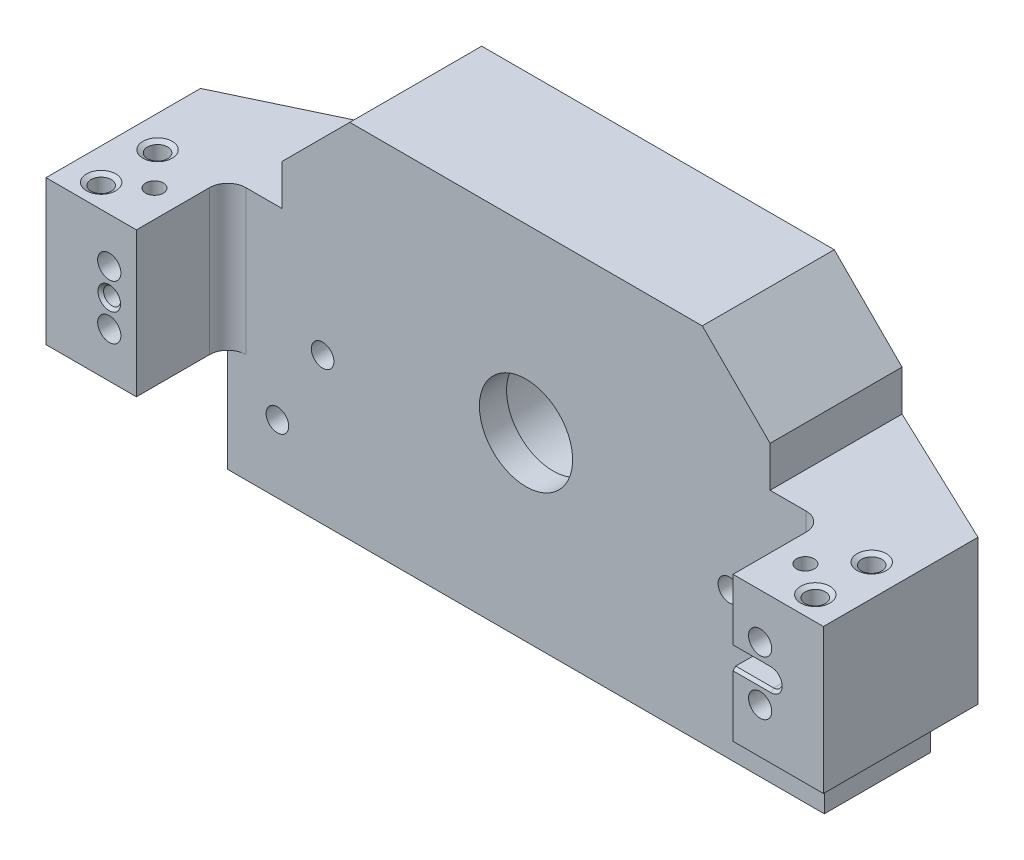
SolidWorks part; units mm, degrees
material "6061-T6 Al"
ref_plane "Front" through (0, 0, 0) normal (0, 0, 1) x (1, 0, 0)
ref_plane "Top" through (0, 0, 0) normal (0, 1, 0) x (1, 0, 0)
ref_plane "Right" through (0, 0, 0) normal (1, 0, 0) x (0, 0, -1)
sketch "Sketch2" plane through (0, 0, 0) normal (0, 1, 0) x (1, 0, 0)
  line L0 (-54.61, -12.7) -> (-54.61, 9.017)
  line L1 (-54.61, 9.017) -> (-34.29, 9.017)
  line L2 (34.29, 18.669) -> (-34.29, 18.669)
  line L3 (-34.29, 9.017) -> (-34.29, 18.669)
  line L4 (34.29, 18.669) -> (34.29, 9.017)
  line L5 (34.29, 9.017) -> (54.61, 9.017)
  line L6 (54.61, 9.017) -> (54.61, -12.7)
  line L7 (-54.61, -12.7) -> (-41.91, -12.7)
  line L8 (-41.91, -12.7) -> (-41.91, 0.127)
  line L9 (-41.91, 0.127) -> (41.91, 0.127)
  line L10 (41.91, 0.127) -> (41.91, -12.7)
  line L11 (41.91, -12.7) -> (54.61, -12.7)
  dimension "D1" = 83.82
  dimension "D2" = 109.22
  dimension "D3" = 31.369
  dimension "D4" = 18.542
  dimension "D5" = 41.91
  dimension "D6" = 18.669
  dimension "D7" = 34.29
  dimension "D8" = 9.652
extrude "Extrude1" add sketch "Sketch2" along normal blind 20.32
sketch "Sketch19" plane through (0, 20.32, 0) normal (0, 1, 0) x (1, 0, 0)
  line L0 (54.61, 9.017) -> (34.29, 9.017) construction
  line L1 (34.29, 9.017) -> (34.29, 18.669) construction
  line L2 (-34.29, 18.669) -> (-34.29, 9.017) construction
  line L3 (-34.29, 9.017) -> (-54.61, 9.017) construction
  line L4 (54.61, 9.017) -> (34.29, 9.017)
  line L5 (34.29, 9.017) -> (34.29, 18.669)
  line L6 (-34.29, 18.669) -> (-34.29, 9.017)
  line L7 (-34.29, 9.017) -> (-54.61, 9.017)
  line L8 (-34.29, 18.669) -> (-54.61, 9.017)
  line L9 (34.29, 18.669) -> (54.61, 9.017)
extrude "Extrude2" add sketch "Sketch19" against normal up to surface (20.32 mm away) up to face at (0, 0, -1.905)
sketch "Sketch24" plane through (0, 20.32, 0) normal (0, 1, 0) x (1, 0, 0)
  line L0 (-41.91, 0.127) -> (41.91, 0.127) construction
  line L1 (34.29, 18.669) -> (-34.29, 18.669)
  line L2 (34.29, 18.669) -> (34.29, 0.127)
  line L3 (34.29, 0.127) -> (-34.29, 0.127)
  line L4 (-34.29, 18.669) -> (-34.29, 0.127)
extrude "Extrude3" add sketch "Sketch24" along normal blind 15.24
sketch "Sketch25" plane through (0, 0, 0) normal (0, -1, 0) x (1, 0, 0)
  line L0 (-41.91, -0.127) -> (41.91, -0.127) construction
  line L1 (-34.29, -18.669) -> (34.29, -18.669)
  line L2 (-41.91, -0.127) -> (-41.91, -15.0495)
  line L3 (-41.91, -0.127) -> (41.91, -0.127)
  line L4 (-41.91, 12.7) -> (-41.91, -0.127) construction
  line L5 (-41.91, -15.0495) -> (-34.29, -18.669)
  line L6 (41.91, -0.127) -> (41.91, -15.0495)
  line L7 (41.91, -0.127) -> (41.91, 12.7) construction
  line L8 (54.61, -9.017) -> (34.29, -18.669) construction
  line L9 (41.91, -15.0495) -> (34.29, -18.669)
  line L10 (-34.29, -18.669) -> (-54.61, -9.017) construction
extrude "Extrude4" add sketch "Sketch25" along normal blind 15.24
sketch "Sketch38" plane through (0, 0, -18.669) normal (0, 0, -1) x (-1, 0, 0)
  circle A0 centre (0, 10.16) radius 17.78
  circle A1 centre (0, 10.16) radius 25.4 construction
  dimension "D1" = 35.56
  dimension "D2" = 50.8
  dimension "D3" = 10.16
extrude "Spherical washer Center Relief" cut sketch "Sketch38" against normal blind 0.762
hole_wizard "Tapped Hole For 1/4-20 Helicoil" positions "Sketch27" profile "Sketch26" tap size "1/4-20" standard "Helicoil® Inch"
sketch "Sketch27" plane through (0, -15.24, 0) normal (0, -1, 0) x (1, 0, 0)
  point P0 (28.575, -6.35)
  point P3 (-28.575, -6.35)
  dimension "D1" = 57.15
  dimension "D2" = 28.575
  dimension "D3" = 6.35
sketch "Sketch26" plane through (28.575, -15.24, -6.35) normal (1, 0, 0) x (0, 0, -1)
  line L0 (0, 0) -> (0, 22.6038)
  line L1 (0, 22.6038) -> (3.3782, 20.574)
  line L2 (3.3782, 20.574) -> (3.3782, 11.684)
  line L3 (3.3782, 11.684) -> (4.0475, 11.684)
  line L5 (4.0475, 11.684) -> (4.0475, 0.0165)
  line L6 (4.0475, 0.0165) -> (4.064, 0)
  line L7 (4.064, 0) -> (0, 0)
  line L8 (-4.0475, 0.0165) -> (-4.064, 0) construction
  line L10 (0, 22.6038) -> (-3.3782, 20.574) construction
  line L11 (0, -6.35) -> (0, 107.95) construction
  dimension "Tap Drill Dia." = 6.7564
  dimension "Tap Drill Depth" = 20.574
  dimension "Thread Major Dia." = 8.095
  dimension "Thread Depth" = 11.684
  dimension "Near C'Sink Dia." = 8.128
  dimension "Near C'Sink Angle" = 90
  dimension "Drill Angle" = 118
sketch "Sketch30" plane through (0, -15.24, 0) normal (0, -1, 0) x (1, 0, 0)
  line L0 (-33.3375, -13.97) -> (-36.5125, -13.97) construction
  line L1 (-33.3375, -15.5651) -> (-36.5125, -15.5651)
  line L2 (-33.3375, -12.3749) -> (-36.5125, -12.3749)
  circle A0 centre (34.925, -13.97) radius 1.5951
  arc A1 (-33.3375, -15.5651) -> (-33.3375, -12.3749) centre (-33.3375, -13.97) ccw
  arc A2 (-36.5125, -12.3749) -> (-36.5125, -15.5651) centre (-36.5125, -13.97) ccw
  circle A3 centre (28.575, -6.35) radius 4.0475 construction
  circle A4 centre (28.575, -6.35) radius 3.3782 construction
  circle A5 centre (-28.575, -6.35) radius 3.3782 construction
  point P4 (-34.925, -13.97)
  dimension "D1" = 6.35
  dimension "D4" = 3.1902
  dimension "D3" = 6.35
  dimension "D2" = 7.62
  dimension "D6" = 3.175
extrude "Pin & Slot Holes" cut sketch "Sketch30" against normal blind 9.525
hole_wizard "#4 Clearance Hole1" positions "Sketch29" profile "Sketch28" hole size "#4" standard "Ansi Inch" end condition through all
sketch "Sketch29" plane through (0, 0, -18.669) normal (0, 0, -1) x (-1, 0, 0)
  line L0 (-31.9532, 5.334) -> (-25.1968, 5.334) construction
  line L1 (25.1968, 5.334) -> (31.9532, 5.334) construction
  point P0 (-28.575, 5.334)
  point P4 (28.575, 5.334)
sketch "Sketch28" plane through (28.575, 5.334, -18.669) normal (1, 0, 0) x (0, 1, 0)
  line L0 (0, 0) -> (0, 31.369)
  line L1 (0, 31.369) -> (1.5875, 31.369)
  line L2 (1.5875, 31.369) -> (1.5875, 0)
  line L5 (1.5875, 0) -> (0, 0)
  line L11 (0, -6.35) -> (0, 107.95) construction
  dimension "Thru Hole Dia." = 3.175
  dimension "Thru Hole Depth" = 31.369
hole_wizard "#4 Clearance Hole2" positions "Sketch33" profile "Sketch32" hole size "#4" standard "Ansi Inch" end condition through all
sketch "Sketch33" plane through (0, 0, -18.669) normal (0, 0, -1) x (-1, 0, 0)
  line L0 (36.5125, -5.715) -> (33.3375, -5.715) construction
  line L1 (-34.925, -5.715) -> (-34.925, -15.24) construction
  line L2 (34.925, -5.715) -> (-34.925, -5.715) construction
  point P0 (-34.925, -5.715)
  point P1 (34.925, -5.715)
sketch "Sketch32" plane through (34.925, -5.715, -18.669) normal (1, 0, 0) x (0, 1, 0)
  line L0 (0, 0) -> (0, 31.369)
  line L1 (0, 31.369) -> (1.5875, 31.369)
  line L2 (1.5875, 31.369) -> (1.5875, 0)
  line L5 (1.5875, 0) -> (0, 0)
  line L11 (0, -6.35) -> (0, 107.95) construction
  dimension "Thru Hole Dia." = 3.175
  dimension "Thru Hole Depth" = 31.369
hole_wizard "CBORE for #4 Socket Head Cap Screw1" positions "Sketch16" profile "Sketch15" counterbore size "#4" standard "Ansi Inch" end condition through all
sketch "Sketch16" plane through (-10.4024, -1.8195, -18.669) normal (0, 0, -1) x (-1, 0, 0)
  line L0 (44.2076, 11.9795) -> (-65.0124, 11.9795) construction
  line L4 (35.3176, 8.1695) -> (35.3176, 11.9795) construction
  line L5 (35.3176, 11.9795) -> (35.3176, 15.7895) construction
  line L7 (-56.1224, 8.1695) -> (-56.1224, 11.9795) construction
  line L8 (-56.1224, 11.9795) -> (-56.1224, 15.7895) construction
  line L9 (44.2076, 22.1395) -> (44.2076, 1.8195) construction
  line L10 (-65.0124, 22.1395) -> (-65.0124, 1.8195) construction
  point P1 (35.3176, 8.1695)
  point P3 (35.3176, 15.7895)
  point P5 (-56.1224, 8.1695)
  point P7 (-56.1224, 15.7895)
  dimension "D1" = 7.62
  dimension "D2" = 7.62
  dimension "D3" = 91.44
  dimension "D4" = 45.72
sketch "Sketch15" plane through (-45.72, 6.35, -18.669) normal (1, 0, 0) x (0, 1, 0)
  line L0 (0, 0) -> (0, 31.369)
  line L1 (0, 31.369) -> (1.6319, 31.369)
  line L3 (1.6319, 31.369) -> (1.6319, 18.2372)
  line L4 (1.6319, 18.2372) -> (2.9718, 18.2372)
  line L5 (2.9718, 18.2372) -> (2.9718, 0)
  line L7 (2.9718, 0) -> (0, 0)
  line L11 (0, -6.35) -> (0, 107.95) construction
  dimension "Thru Hole Dia." = 3.2639
  dimension "Thru Hole Depth" = 31.369
  dimension "C'Bore Dia." = 5.9436
  dimension "C'Bore Depth" = 18.2372
hole_wizard "Tapped Hole for 1/2-13  Helicoil1" positions "Sketch23" profile "Sketch22" tap size "1/2-13" standard "Helicoil® Inch" end condition through all
sketch "Sketch23" plane through (0, 0, -18.669) normal (0, 0, -1) x (-1, 0, 0)
  point P0 (0, 10.16)
  dimension "D1" = 10.16
sketch "Sketch22" plane through (0, 10.16, -18.669) normal (1, 0, 0) x (0, 1, 0)
  line L0 (0, 0) -> (0, 31.369)
  line L1 (6.5481, 30.3527) -> (8.3083, 31.369)
  line L2 (7.6733, 14.732) -> (6.5481, 14.732)
  line L3 (6.5481, 14.732) -> (6.5481, 30.3527)
  line L5 (7.6733, 14.732) -> (7.6733, 0.3666)
  line L6 (7.6733, 0.3666) -> (8.3083, 0)
  line L7 (8.3083, 0) -> (0, 0)
  line L8 (-7.6733, 0.3666) -> (-8.3083, 0) construction
  line L11 (0, -6.35) -> (0, 107.95) construction
  line L12 (8.3083, 31.369) -> (0, 31.369)
  line L13 (-6.5481, 30.3527) -> (-8.3083, 31.369) construction
  dimension "Thru Tap Drill Dia." = 13.0962
  dimension "Thru Tap Drill Depth" = 31.369
  dimension "Thread Major Dia." = 15.3467
  dimension "Thread Depth" = 14.732
  dimension "Near C'Sink Dia." = 16.6167
  dimension "Near C'Sink Angle" = 120
  dimension "Far C'Sink Dia." = 16.6167
  dimension "Far C'Sink Angle" = 120
hole_wizard "#40 (0.098) Diameter Hole0" positions "Sketch37" profile "Sketch36" hole size "#40" standard "Ansi Inch" end condition through all
sketch "Sketch37" plane through (0, 20.32, 0) normal (0, 1, 0) x (-1, 0, 0)
  line L0 (45.72, 12.7) -> (45.72, -0.4318) construction
  line L1 (54.61, 12.7) -> (41.91, 12.7) construction
  line L2 (-45.72, 12.7) -> (-45.72, -0.4318) construction
  point P0 (45.72, 6.35)
  point P6 (-45.72, 6.35)
  dimension "D1" = 6.35
sketch "Sketch36" plane through (-45.72, 20.32, 6.35) normal (1, 0, 0) x (0, 0, 1)
  line L0 (0, 0) -> (0, 35.56)
  line L1 (0, 35.56) -> (1.2446, 35.56)
  line L2 (1.2446, 35.56) -> (1.2446, 0)
  line L5 (1.2446, 0) -> (0, 0)
  line L11 (0, -6.35) -> (0, 107.95) construction
  dimension "Thru Hole Dia." = 2.4892
  dimension "Thru Hole Depth" = 35.56
hole_wizard "#4-40 Tapped Hole1" positions "Sketch21" profile "Sketch20" tap size "#4-40" standard "Ansi Inch" end condition up to next
sketch "Sketch21" plane through (0, 20.32, 0) normal (0, 1, 0) x (-1, 0, 0)
  point P0 (50.165, 9.398)
  point P2 (50.165, 1.4732)
  point P4 (-50.165, 1.4732)
  point P6 (-50.165, 9.398)
  dimension "D1" = 100.33
  dimension "D2" = 50.165
  dimension "D3" = 9.398
  dimension "D4" = 7.9248
sketch "Sketch20" plane through (-50.165, 20.32, 9.398) normal (1, 0, 0) x (0, 0, 1)
  line L0 (0, 0) -> (0, 20.32)
  line L1 (0, 20.32) -> (2.0574, 20.32)
  line L2 (1.4224, 19.9534) -> (1.4224, 0.3666)
  line L3 (1.4224, 0.3666) -> (2.0574, 0)
  line L5 (2.0574, 0) -> (0, 0)
  line L6 (-1.4224, 0.3666) -> (-2.0574, 0) construction
  line L7 (2.0574, 20.32) -> (1.4224, 19.9534)
  line L8 (-2.0574, 20.32) -> (-1.4224, 19.9534) construction
  line L11 (0, -6.35) -> (0, 107.95) construction
  dimension "Thread Major Dia." = 2.8448
  dimension "Thru Tap Drill Depth" = 20.32
  dimension "Near C'Sink Dia." = 4.1148
  dimension "Near C'Sink Angle" = 120
  dimension "Far C'Sink Dia." = 4.1148
  dimension "Far C'Sink Angle" = 120
chamfer "Chamfer1" distance 9.525 angle 45 2 edges at (34.29, 35.56, -9.398) (-34.29, 35.56, -9.398)
fillet "Fillet1" radius 2.54 2 edges at (-41.91, 10.16, -0.127) (41.91, 10.16, -0.127)
chamfer "Chamfer2" distance 0.9906 angle 45 5 edges at (-34.925, -15.24, -15.5651) (-38.1076, -15.24, -13.97) (-34.925, -15.24, -12.3749) (-31.7424, -15.24, -13.97) (34.925, -15.24, -15.5651)
sketch "Sketch39" plane through (0, 0, 12.7) normal (0, 0, 1) x (1, 0, 0)
  circle A0 centre (45.72, 10.16) radius 0.8014
  circle A1 centre (-45.72, 10.16) radius 0.9436
hole_wizard "#4 Clearance Hole3" positions "Sketch43" profile "Sketch42" hole size "#4" standard "Ansi Inch"
sketch "Sketch43" plane through (0, 0, 12.7) normal (0, 0, 1) x (1, 0, 0)
  line L0 (-45.72, 13.97) -> (-45.72, 6.35) construction
  point P0 (-45.72, 10.16)
sketch "Sketch42" plane through (-45.72, 10.16, 12.7) normal (1, 0, 0) x (0, -1, 0)
  line L0 (0, 0) -> (0, 7.0673)
  line L1 (0, 7.0673) -> (1.1938, 6.35)
  line L2 (1.1938, 6.35) -> (1.1938, 0.3937)
  line L3 (1.1938, 0.3937) -> (1.5875, 0)
  line L5 (1.5875, 0) -> (0, 0)
  line L6 (-1.1938, 0.3937) -> (-1.5875, 0) construction
  line L10 (0, 7.0673) -> (-1.1938, 6.35) construction
  line L11 (0, -6.35) -> (0, 107.95) construction
  dimension "Hole Dia." = 2.3876
  dimension "Hole Depth" = 6.35
  dimension "Near C'Sink Dia." = 3.175
  dimension "Near C'Sink Angle" = 90
  dimension "Drill Angle" = 118
sketch "Sketch44" plane through (0, 0, 12.7) normal (0, 0, 1) x (1, 0, 0)
  line L0 (45.72, 10.16) -> (47.244, 10.16) construction
  line L1 (41.91, 11.3538) -> (47.244, 11.3538)
  line L2 (41.91, 8.9662) -> (47.244, 8.9662)
  line L3 (45.72, 6.35) -> (45.72, 13.97) construction
  line L4 (41.91, 11.3538) -> (41.91, 8.9662)
  line L5 (41.91, 20.32) -> (41.91, 0) construction
  line L6 (45.72, 10.16) -> (41.91, 10.16) construction
  circle A0 centre (-45.72, 10.16) radius 1.1938 construction
  arc A1 (47.244, 8.9662) -> (47.244, 11.3538) centre (47.244, 10.16) ccw
  point P2 (46.6046, 10.16)
  dimension "D1" = 1.524
extrude "Extrude5" cut sketch "Sketch44" against normal blind 6.35
chamfer "Chamfer3" distance 0.381 angle 45 3 edges at (44.577, 8.9662, 12.7) (44.577, 11.3538, 12.7) (48.4378, 10.16, 12.7)
